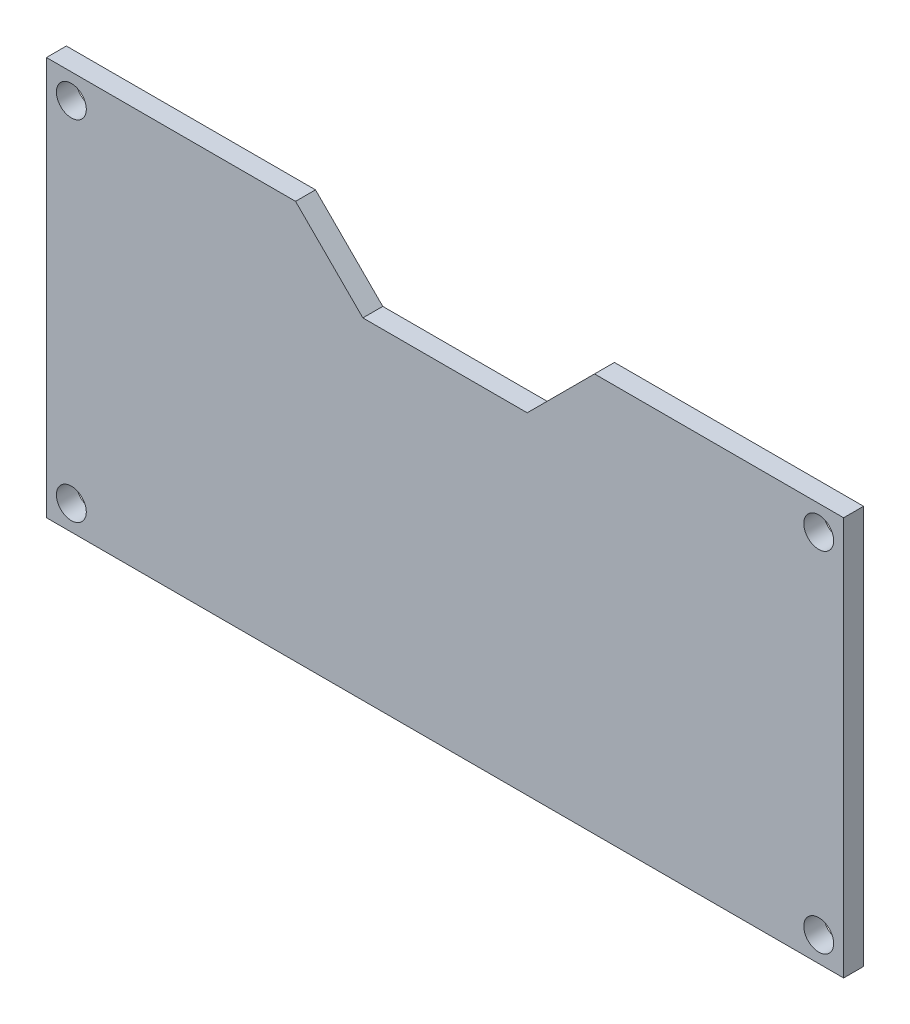
SolidWorks part; units mm, degrees
ref_plane "Plan de face" through (0, 0, 0) normal (0, 0, 1) x (1, 0, 0)
ref_plane "Plan de dessus" through (0, 0, 0) normal (0, 1, 0) x (1, 0, 0)
ref_plane "Plan de droite" through (0, 0, 0) normal (1, 0, 0) x (0, 0, -1)
sketch "Esquisse1" plane through (0, 0, 0) normal (0, 0, 1) x (1, 0, 0)
  line L1 (0, 0) -> (80, 0)
  line L2 (0, 0) -> (0, 40)
  line L3 (0, 40) -> (80, 40)
  line L4 (80, 0) -> (80, 40)
  dimension "D1" = 80
  dimension "D2" = 40
extrude "Boss.-Extru.1" add sketch "Esquisse1" along normal blind 2
sketch "Esquisse2" plane through (0, 0, 2) normal (0, 0, 1) x (1, 0, 0)
  line L0 (0, 0) -> (80, 0) construction
  line L1 (2.5, 37.5) -> (77.5, 37.5) construction
  line L2 (2.5, 37.5) -> (2.5, 2.5) construction
  line L3 (2.5, 2.5) -> (77.5, 2.5) construction
  line L4 (77.5, 37.5) -> (77.5, 2.5) construction
  line L5 (0, 40) -> (0, 0) construction
  circle A0 centre (2.5, 37.5) radius 1.5
  circle A1 centre (77.5, 37.5) radius 1.5
  circle A2 centre (2.5, 2.5) radius 1.5
  circle A3 centre (77.5, 2.5) radius 1.5
  dimension "D1" = 35
  dimension "D2" = 2.5
  dimension "D3" = 75
  dimension "D4" = 2.5
extrude "Enlèv. mat.-Extru.1" cut sketch "Esquisse2" against normal blind 2
sketch "Esquisse3" plane through (0, 0, 0) normal (0, 0, -1) x (-1, 0, 0)
  line L0 (-25, 40) -> (-55, 40)
  line L1 (-80, 40) -> (0, 40) construction
  line L2 (-55, 40) -> (-48.2463, 33.2463)
  line L3 (-48.2463, 33.2463) -> (-31.7537, 33.2463)
  line L4 (-31.7537, 33.2463) -> (-25, 40)
  dimension "D1" = 45
  dimension "D2" = 45
  dimension "D3" = 30
  dimension "D4" = 25
extrude "Enlèv. mat.-Extru.2" cut sketch "Esquisse3" against normal blind 10
